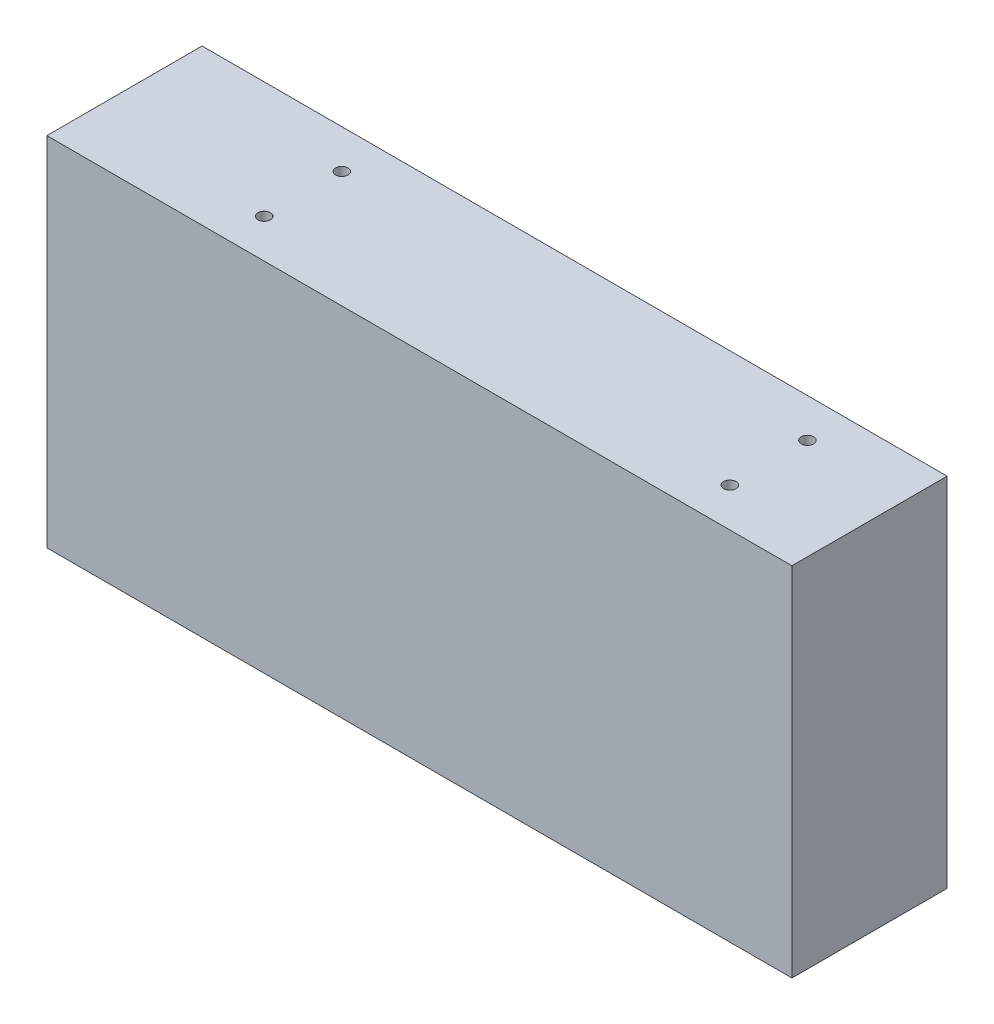
SolidWorks part; units mm, degrees
ref_plane "前视基准面" through (0, 0, 0) normal (0, 0, 1) x (1, 0, 0)
ref_plane "上视基准面" through (0, 0, 0) normal (0, 1, 0) x (1, 0, 0)
ref_plane "右视基准面" through (0, 0, 0) normal (1, 0, 0) x (0, 0, -1)
sketch "草图1" plane through (0, 0, 0) normal (0, 0, 1) x (1, 0, 0)
  line L1 (-117.0572, 61.7984) -> (122.9428, 61.7984)
  line L2 (-117.0572, 61.7984) -> (-117.0572, -53.2016)
  line L3 (-117.0572, -53.2016) -> (122.9428, -53.2016)
  line L4 (122.9428, 61.7984) -> (122.9428, -53.2016)
  dimension "D1" = 240
  dimension "D2" = 115
extrude "凸台-拉伸1" add sketch "草图1" along normal blind 50
sketch "草图2" plane through (0, 0, 0) normal (0, 0, -1) x (-1, 0, 0)
  circle A0 centre (-90.4428, 29.2984) radius 2
  circle A1 centre (59.5572, 29.2984) radius 2
  circle A2 centre (59.5572, -20.7016) radius 2
  circle A3 centre (-90.4428, -20.7016) radius 2
  dimension "D5" = 4
  dimension "D6" = 4
  dimension "D7" = 4
  dimension "D8" = 4
extrude "切除-拉伸1" cut sketch "草图2" against normal blind 5
sketch "草图3" plane through (0, 61.7984, 0) normal (0, 1, 0) x (1, 0, 0)
  circle A0 centre (90.4428, -37.5) radius 2
  circle A1 centre (-59.5572, -37.5) radius 2
  circle A2 centre (-59.5572, -12.5) radius 2
  circle A3 centre (90.4428, -12.5) radius 2
  dimension "D5" = 4
  dimension "D6" = 4
  dimension "D7" = 4
  dimension "D8" = 4
extrude "切除-拉伸2" cut sketch "草图3" against normal blind 6
